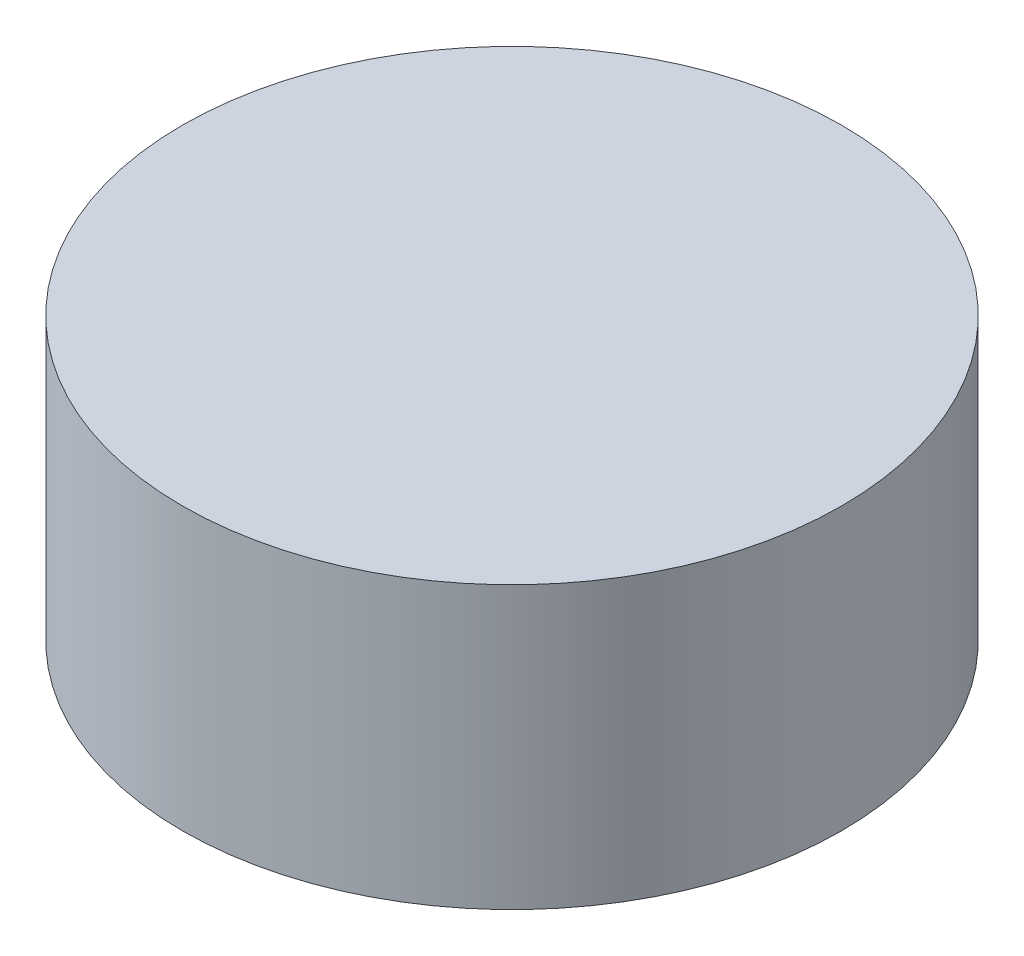
SolidWorks part; units mm, degrees
ref_plane "Front Plane" through (0, 0, 0) normal (0, 0, 1) x (1, 0, 0)
ref_plane "Top Plane" through (0, 0, 0) normal (0, 1, 0) x (1, 0, 0)
ref_plane "Right Plane" through (0, 0, 0) normal (1, 0, 0) x (0, 0, -1)
sketch "Sketch1" plane through (0, 0, 0) normal (0, 1, 0) x (1, 0, 0)
  circle A0 centre (0, 0) radius 9.525
  dimension "D1" = 19.05
extrude "Boss-Extrude1" add sketch "Sketch1" along normal blind 8.128
